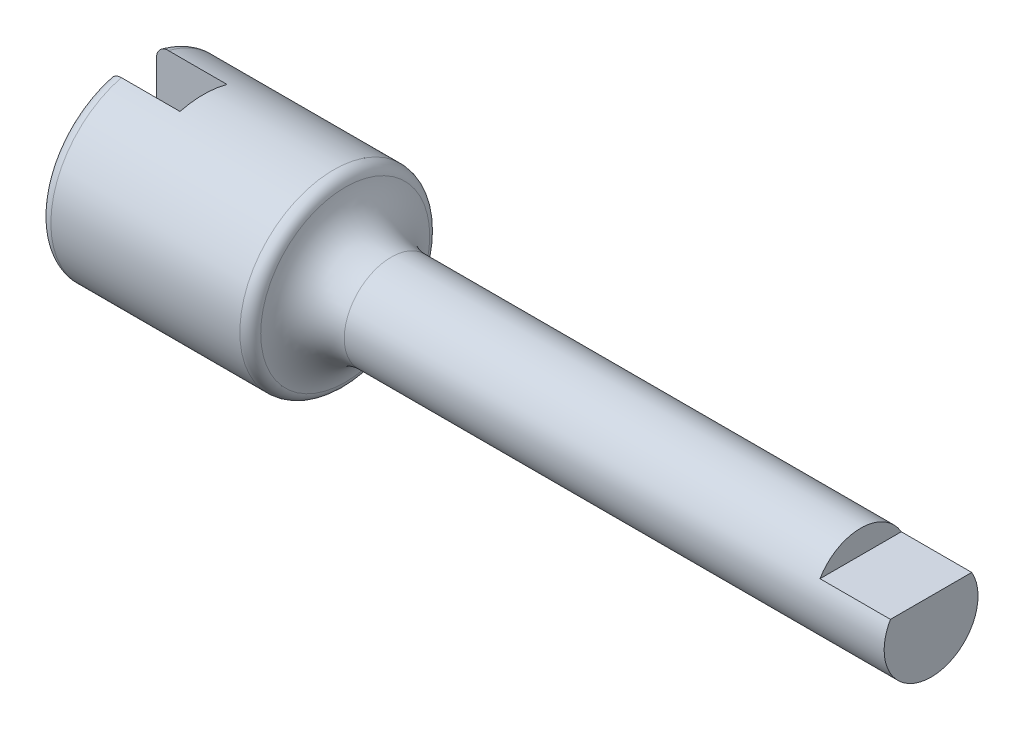
SolidWorks part; units mm, degrees
ref_plane "Front Plane" through (0, 0, 0) normal (0, 0, 1) x (1, 0, 0)
ref_plane "Top Plane" through (0, 0, 0) normal (0, 1, 0) x (1, 0, 0)
ref_plane "Right Plane" through (0, 0, 0) normal (1, 0, 0) x (0, 0, -1)
sketch "Sketch1" plane through (0, 0, 0) normal (0, 0, 1) x (1, 0, 0)
  line L0 (0, 0) -> (43.4623, 0) construction
  line L1 (0, 0) -> (0, 4)
  line L2 (0, 4) -> (9, 4)
  line L4 (11, 2) -> (34, 2)
  line L5 (34, 2) -> (34, 0)
  line L6 (34, 0) -> (0, 0)
  arc A0 (9, 4) -> (11, 2) centre (11, 4) ccw
  dimension "D1" = 4
  dimension "D2" = 2
  dimension "D3" = 4
  dimension "D4" = 9
  dimension "D5" = 25
revolve "Revolve1" add sketch "Sketch1" angle 360 about L0
sketch "Sketch2" plane through (0, 0, 0) normal (-1, 0, 0) x (0, 0, 1)
  line L0 (-1, 4) -> (1, -4) construction
  line L1 (-1, 4) -> (1, 4)
  line L2 (-1, 4) -> (-1, -4)
  line L3 (-1, -4) -> (1, -4)
  line L4 (1, 4) -> (1, -4)
  circle A0 centre (0, 0) radius 4 construction
  dimension "D1" = 2
extrude "Cut-Extrude1" cut sketch "Sketch2" against normal blind 3
fillet "Fillet1" radius 0.5 3 edges at (0, 0, 4) (0, 0, -4) (9, 0, 4)
sketch "Sketch3" plane through (0, 0, 0) normal (0, 0, 1) x (1, 0, 0)
  line L0 (34, -2) -> (34, 2) construction
  line L1 (34, 2) -> (31, 2)
  line L2 (34, 2) -> (34, 1)
  line L3 (34, 1) -> (31, 1)
  line L4 (31, 2) -> (31, 1)
  dimension "D1" = 3
  dimension "D2" = 1
extrude "Cut-Extrude2" cut sketch "Sketch3" against normal mid plane 8
